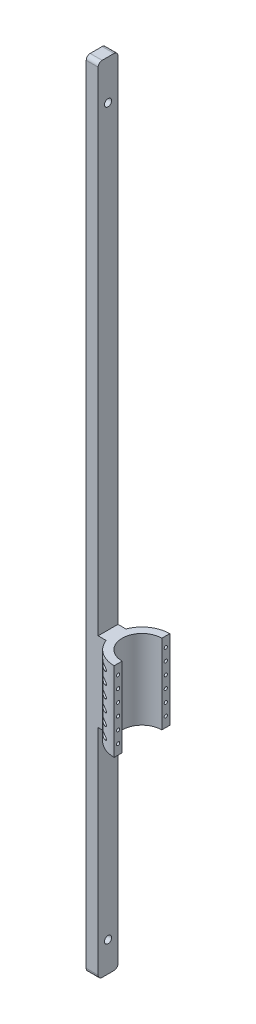
SolidWorks part; units mm, degrees
ref_plane "Front Plane" through (0, 0, 0) normal (0, 0, 1) x (1, 0, 0)
ref_plane "Top Plane" through (0, 0, 0) normal (0, 1, 0) x (1, 0, 0)
ref_plane "Right Plane" through (0, 0, 0) normal (1, 0, 0) x (0, 0, -1)
sketch "Çizim1" plane through (0, 0, 0) normal (0, 1, 0) x (1, 0, 0)
  line L0 (0, 140) -> (0, 100)
  line L1 (0, -100) -> (0, -140)
  line L2 (-130.767, -50) -> (-170.767, -50)
  line L3 (-170.767, -50) -> (-170.767, 50)
  line L4 (-170.767, 50) -> (-130.767, 50)
  arc A0 (0, 100) -> (0, -100) centre (0, 0) ccw
  arc A1 (0, 140) -> (0, -140) centre (0, 0) ccw
  point P12 (-140, 0)
  point P13 (-100, 0)
  point P14 (-170.767, 0)
  dimension "D1" = 40
  dimension "D2" = 140
  dimension "D3" = 100
  dimension "D4" = 50
  dimension "D5" = 50
extrude "Yükseklik-Ekstrüzyon2" add sketch "Çizim1" along normal blind 400 contours L0 A1 L1 A0 | A1 L4 L3 L2
ref_plane "Düzlem2" through (-150.77, 0, 0) normal (1, 0, 0) x (0, 0, -1)
sketch "Çizim5" plane through (-170.767, 0, 0) normal (-1, 0, 0) x (0, 0, 1)
  line L1 (50, 0) -> (50, 2880)
  line L2 (30, 2900) -> (-30, 2900)
  line L3 (-50, 2880) -> (-50, -1080)
  line L4 (-30, -1100) -> (30, -1100)
  line L5 (50, -1080) -> (50, 0)
  arc A0 (-30, -1100) -> (-50, -1080) centre (-30, -1080) cw
  arc A1 (30, -1100) -> (50, -1080) centre (30, -1080) ccw
  arc A2 (-50, 2880) -> (-30, 2900) centre (-30, 2880) cw
  arc A3 (50, 2880) -> (30, 2900) centre (30, 2880) ccw
  point P4 (-50, -1100)
  point P14 (-50, 2900)
  dimension "D3" = 20
  dimension "D1" = 2500
  dimension "D2" = 1500
extrude "Yükseklik-Ekstrüzyon3" add sketch "Çizim5" along normal blind 60
ref_plane "Düzlem3" through (0, 0, 0) normal (1, 0, 0) x (0, 0, -1)
sketch "Çizim6" plane through (0, 0, 0) normal (1, 0, 0) x (0, 0, -1)
  line L0 (-120, 403.9946) -> (-120, -45.3014) construction
  line L1 (-100, 400) -> (-140, 400) construction
  circle A0 centre (-120, 350) radius 8
  circle A1 centre (-120, 290) radius 8
  circle A2 centre (-120, 230) radius 8
  circle A3 centre (-120, 170) radius 8
  circle A4 centre (-120, 110) radius 8
  circle A5 centre (-120, 50) radius 8
  dimension "D1" = 16
  dimension "D3" = 60
  dimension "D7" = 60
  dimension "D2" = 50
  dimension "D4" = 60
  dimension "D5" = 60
  dimension "D6" = 60
extrude "Kes-Ekstrüzyon1" cut sketch "Çizim6" against normal blind 30
ref_plane "Düzlem6" through (0, 0, 0) normal (1, 0, 0) x (0, 0, -1)
sketch "Çizim7" plane through (0, 0, 0) normal (1, 0, 0) x (0, 0, -1)
  line L0 (120, 428.1625) -> (120, -49.589) construction
  line L1 (140, 400) -> (100, 400) construction
  circle A0 centre (120, 350) radius 8
  circle A1 centre (120, 290) radius 8
  circle A2 centre (120, 230) radius 8
  circle A3 centre (120, 170) radius 8
  circle A4 centre (120, 110) radius 8
  circle A5 centre (120, 50) radius 8
  dimension "D1" = 50
  dimension "D2" = 60
  dimension "D3" = 60
  dimension "D4" = 60
  dimension "D5" = 60
  dimension "D6" = 60
extrude "Kes-Ekstrüzyon2" cut sketch "Çizim7" against normal blind 30
ref_plane "Düzlem7" through (-30, 0, 0) normal (1, 0, 0) x (0, 0, -1)
sketch "Çizim10" plane through (-30, 0, 0) normal (1, 0, 0) x (0, 0, -1)
  line L0 (0, 416.67) -> (0, -77.3161) construction
  circle A0 centre (-120, 350) radius 12
  circle A1 centre (-120, 290) radius 12
  circle A2 centre (-120, 230) radius 12
  circle A3 centre (-120, 170) radius 12
  circle A4 centre (-120, 110) radius 12
  circle A5 centre (-120, 50) radius 12
  circle A6 centre (120, 50) radius 12
  circle A7 centre (120, 110) radius 12
  circle A8 centre (120, 170) radius 12
  circle A9 centre (120, 230) radius 12
  circle A10 centre (120, 290) radius 12
  circle A11 centre (120, 350) radius 12
extrude "Kes-Ekstrüzyon6" cut sketch "Çizim10" against normal blind 170
sketch "Çizim11" plane through (-230.767, 0, 0) normal (-1, 0, 0) x (0, 0, 1)
  line L0 (0, 2900) -> (0, -1790.505) construction
  line L1 (30, 2900) -> (-30, 2900) construction
  line L2 (-140, 0) -> (-50, 0) construction
  circle A0 centre (0, 320) radius 18
  circle A1 centre (0, 200) radius 18
  circle A2 centre (0, 80) radius 18
  dimension "D1" = 120
  dimension "D2" = 120
  dimension "D3" = 80
extrude "Kes-Ekstrüzyon7" cut sketch "Çizim11" against normal blind 80
sketch "Çizim12" plane through (-230.767, 0, 0) normal (-1, 0, 0) x (0, 0, 1)
  line L0 (0, -1100) -> (0, -813.979) construction
  line L1 (-30, -1100) -> (30, -1100) construction
  circle A0 centre (0, -950) radius 18
  dimension "D1" = 150
extrude "Kes-Ekstrüzyon8" cut sketch "Çizim12" against normal blind 60
sketch "Çizim14" plane through (-230.767, 0, 0) normal (-1, 0, 0) x (0, 0, 1)
  line L0 (0, 2900) -> (0, 2307.5824) construction
  line L1 (30, 2900) -> (-30, 2900) construction
  circle A0 centre (0, 2700) radius 18
  dimension "D1" = 200
extrude "Kes-Ekstrüzyon9" cut sketch "Çizim14" against normal blind 128
